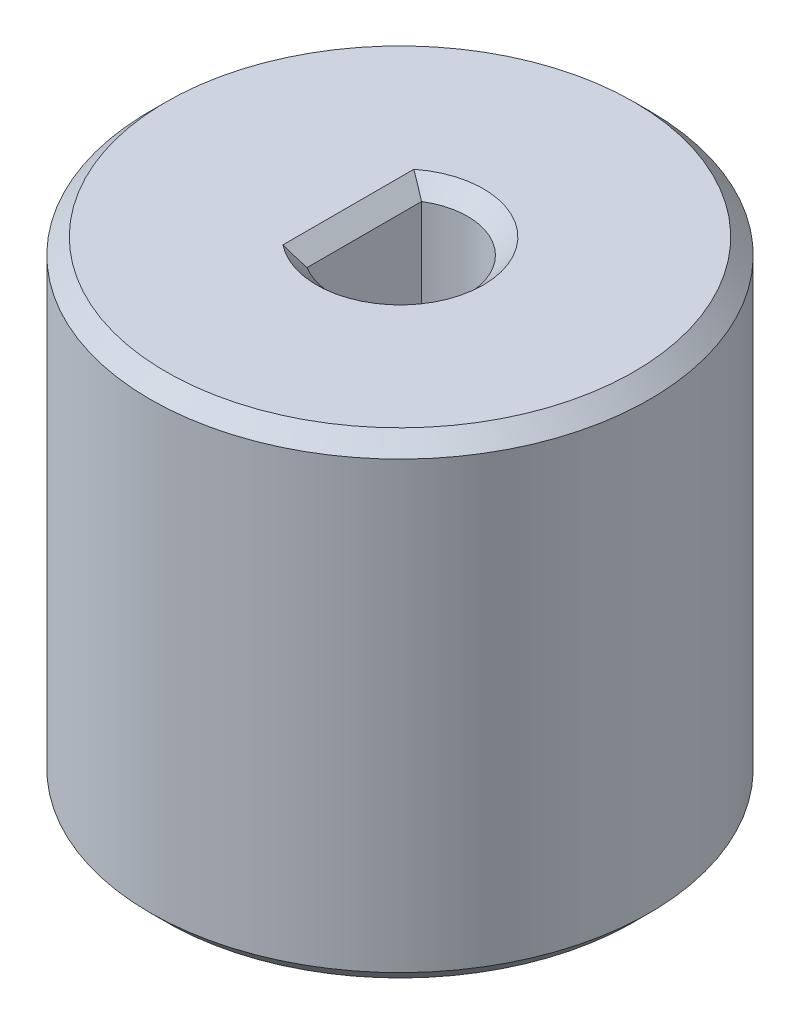
SolidWorks part; units mm, degrees
ref_plane "Alzado" through (0, 0, 0) normal (0, 0, 1) x (1, 0, 0)
ref_plane "Planta" through (0, 0, 0) normal (0, 1, 0) x (1, 0, 0)
ref_plane "Vista lateral" through (0, 0, 0) normal (1, 0, 0) x (0, 0, -1)
sketch "Croquis2" plane through (0, 0, 0) normal (0, 0, 1) x (1, 0, 0)
  line L0 (0, 0) -> (0, 30) construction
  line L1 (-4.25, 30) -> (-14.725, 30)
  line L2 (-12.725, 1) -> (-12.725, 14)
  line L3 (-11.725, 15) -> (-4.25, 15)
  line L4 (-4.25, 15) -> (-4.25, 30)
  line L6 (-14.725, 0) -> (-13.725, 0)
  line L7 (0, 0) -> (-25.5548, 0) construction
  line L10 (-15.725, 29) -> (-15.725, 1)
  line L11 (-14.725, 30) -> (-15.725, 29)
  line L12 (-12.725, 14) -> (-11.725, 15)
  line L13 (-15.725, 1) -> (-14.725, 0)
  line L15 (-13.725, 0) -> (-12.725, 1)
  point P4 (-12.725, 15)
  point P5 (-12.725, 0)
  point P8 (-15.725, 0)
  point P12 (-15.725, 30)
  dimension "D1" = 25.45
  dimension "D2" = 8.5
  dimension "D3" = 15
  dimension "D4" = 15
  dimension "D5" = 3
revolve "Revolución1" add sketch "Croquis2" angle 360 about L0
sketch "Croquis3" plane through (0, 30, 0) normal (0, 1, 0) x (1, 0, 0)
  line L0 (0, 0) -> (-4.25, 0) construction
  line L1 (0, 0) -> (0, 4.25) construction
  line L2 (-6.25, 3.6056) -> (-2.25, 3.6056)
  line L3 (-6.25, 3.6056) -> (-6.25, -3.6056)
  line L4 (-6.25, -3.6056) -> (-2.25, -3.6056)
  line L5 (-2.25, 3.6056) -> (-2.25, -3.6056)
  line L6 (-6.25, 3.6056) -> (-2.25, -3.6056) construction
  line L7 (-6.25, -3.6056) -> (-2.25, 3.6056) construction
  circle A0 centre (0, 0) radius 4.25 construction
  dimension "D1" = 4
extrude "Saliente-Extruir1" add sketch "Croquis3" against normal blind 15
chamfer "Chaflán1" distance 1 angle 45 2 edges at (4.25, 30, 0) (-2.25, 30, 0)
